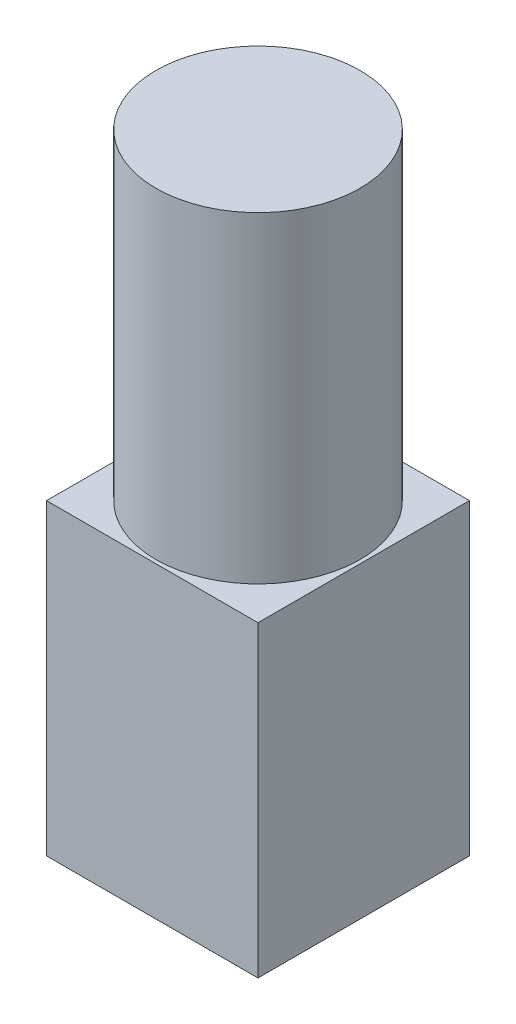
SolidWorks part; units mm, degrees
ref_plane "Front Plane" through (0, 0, 0) normal (0, 0, 1) x (1, 0, 0)
ref_plane "Top Plane" through (0, 0, 0) normal (0, 1, 0) x (1, 0, 0)
ref_plane "Right Plane" through (0, 0, 0) normal (1, 0, 0) x (0, 0, -1)
sketch "Sketch2" plane through (0, 0, 0) normal (0, 1, 0) x (1, 0, 0)
  line L1 (0, 0) -> (29, 0)
  line L2 (0, 0) -> (0, -29)
  line L3 (0, -29) -> (29, -29)
  line L4 (29, 0) -> (29, -29)
  dimension "D1" = 29
  dimension "D2" = 29
extrude "Boss-Extrude4" add sketch "Sketch2" along normal blind 42.2
sketch "Sketch3" plane through (0, 42.2, 0) normal (0, 1, 0) x (1, 0, 0)
  line L0 (0, 0) -> (29, -29) construction
  circle A0 centre (14.5, -14.5) radius 14
  dimension "D1" = 28
extrude "Boss-Extrude5" add sketch "Sketch3" along normal blind 44.1
